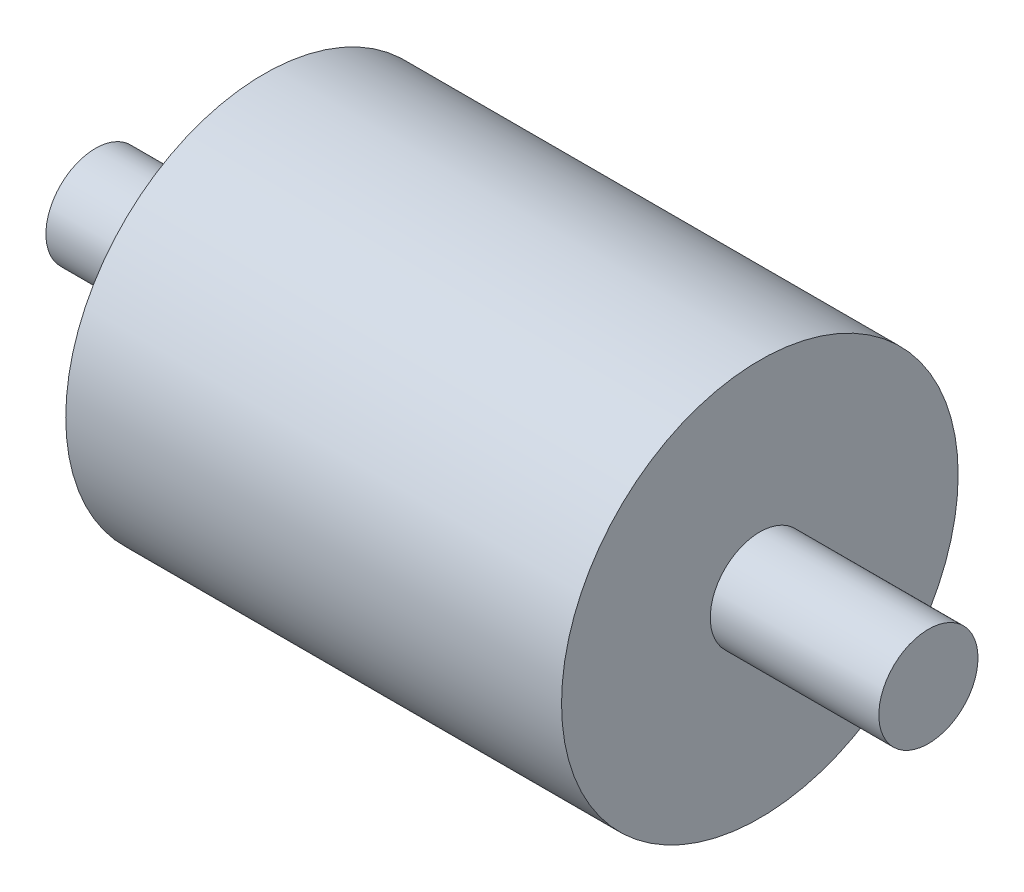
SolidWorks part; units mm, degrees
ref_plane "Front" through (0, 0, 0) normal (0, 0, 1) x (1, 0, 0)
ref_plane "Top" through (0, 0, 0) normal (0, 1, 0) x (1, 0, 0)
ref_plane "Right" through (0, 0, 0) normal (1, 0, 0) x (0, 0, -1)
sketch "草图1" plane through (0, 0, 0) normal (1, 0, 0) x (0, 0, -1)
  circle A0 centre (0, 0) radius 20
extrude "凸台-拉伸1" add sketch "草图1" along normal mid plane 50
sketch "草图2" plane through (0, 0, 0) normal (1, 0, 0) x (0, 0, -1)
  circle A0 centre (0, 0) radius 5
extrude "凸台-拉伸2" add sketch "草图2" along normal mid plane 84
